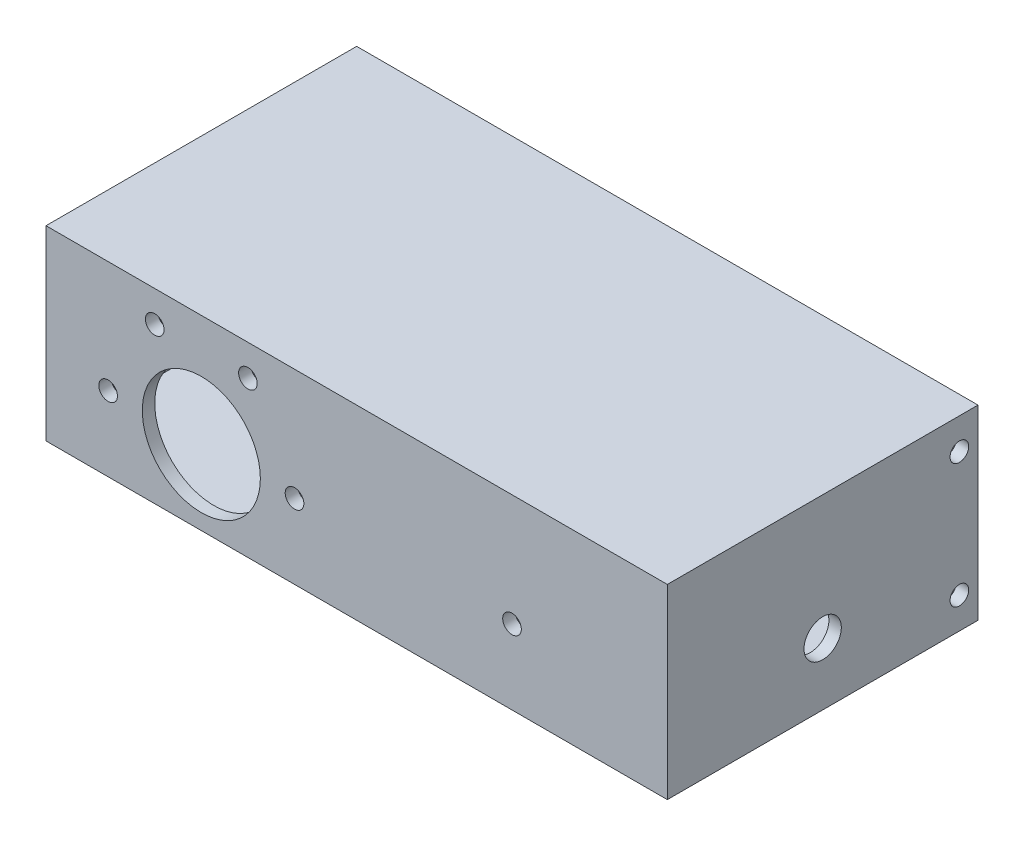
SolidWorks part; units mm, degrees
ref_plane "Front Plane" through (0, 0, 0) normal (0, 0, 1) x (1, 0, 0)
ref_plane "Top Plane" through (0, 0, 0) normal (0, 1, 0) x (1, 0, 0)
ref_plane "Right Plane" through (0, 0, 0) normal (1, 0, 0) x (0, 0, -1)
sketch "Sketch1" plane through (0, 0, 0) normal (0, 0, 1) x (1, 0, 0)
  line L0 (-40, -3) -> (-10, -3) construction
  line L1 (-50, -15) -> (50, -15)
  line L2 (-50, -15) -> (-50, 15)
  line L3 (-50, 15) -> (50, 15)
  line L4 (50, -15) -> (50, 15)
  line L5 (-50, -15) -> (50, 15) construction
  line L6 (-50, 15) -> (50, -15) construction
  circle A0 centre (-25, -3) radius 9.5
  arc A1 (-40, -3) -> (-10, -3) centre (-25, -3) cw construction
  circle A2 centre (-40, -3) radius 1.5
  circle A3 centre (-32.5, 9.9904) radius 1.5
  circle A4 centre (-17.5, 9.9904) radius 1.5
  circle A5 centre (-10, -3) radius 1.5
  circle A6 centre (25, -3) radius 1.5
  point P0 (0, 0)
  dimension "D1" = 19
  dimension "D7" = 3
  dimension "D12" = 3
  dimension "D2" = 100
  dimension "D3" = 30
  dimension "D4" = 12
  dimension "D5" = 25
  dimension "D6" = 30
  dimension "D9" = 12.9904
  dimension "D10" = 7.5
  dimension "D11" = 12.9904
  dimension "D13" = 12
  dimension "D14" = 25
  dimension "D8" = 4
extrude "Boss-Extrude1" add sketch "Sketch1" along normal blind 2
sketch "Sketch2" plane through (0, 0, 2) normal (0, 0, 1) x (1, 0, 0)
  line L0 (-48, 0) -> (-33, 0) construction
  line L1 (-37.5559, 12) -> (-20.1698, 12) construction
  line L2 (-20.1698, 12) -> (-12.0117, 12) construction
  line L3 (-12.6804, 0) -> (-5.2802, 0) construction
  line L4 (-50, -15) -> (50, -15) construction
  line L5 (-50, 15) -> (-50, -15) construction
  line L6 (25, 0) -> (40, 0)
  line L7 (40, 0) -> (15, 0) construction
  line L8 (50, -15) -> (50, 15) construction
  line L10 (50, 15) -> (-50, 15) construction
  line L11 (-48, -13) -> (48, -13)
  line L12 (-48, -13) -> (-48, 13)
  line L13 (-48, 13) -> (48, 13)
  line L14 (48, -13) -> (48, 13)
  line L15 (-48, -13) -> (48, 13) construction
  line L16 (-48, 13) -> (48, -13) construction
  line L18 (-50, -15) -> (50, -15)
  line L19 (-50, -15) -> (-50, 15)
  line L20 (-50, 15) -> (50, 15)
  line L21 (50, -15) -> (50, 15)
  line L22 (-50, -15) -> (50, 15) construction
  line L23 (-50, 15) -> (50, -15) construction
  text T0 "Disengaged" font "Century Gothic" height 1.5
  text T1 "        1" font "Century Gothic" height 1.5
  text T2 "   2" font "Century Gothic" height 1.5
  text T3 "    3" font "Century Gothic" height 1.5
  text T4 "Dead Mans Switch          " font "Century Gothic" height 1.5
  line M7 (50, -15) -> (50, 15)
  line M8 (50, 15) -> (-50, 15)
  line M9 (-50, 15) -> (-50, -15)
  line M10 (-50, -15) -> (50, -15)
  dimension "D1" = 15
  dimension "D2" = 27
  dimension "D3" = 2
  dimension "D4" = 12.4441
  dimension "D5" = 29.8302
  dimension "D6" = 37.3196
  dimension "D7" = 15
  dimension "D8" = 25
  dimension "D9" = 15
  dimension "D10" = 35
  dimension "D11" = 2
  dimension "D12" = 2
  dimension "D13" = 2
  dimension "D14" = 2
extrude "Boss-Extrude3" add sketch "Sketch2" against normal blind 50 contours L14 L11 L12 L13 M10 M7 M8 M9
sketch "Sketch3" plane through (0, 0, -48) normal (0, 0, -1) x (-1, 0, 0)
  line L1 (-50, -15) -> (50, -15)
  line L2 (-50, -15) -> (-50, 15)
  line L3 (-50, 15) -> (50, 15)
  line L4 (50, -15) -> (50, 15)
  line L5 (-50, -15) -> (50, 15) construction
  line L6 (-50, 15) -> (50, -15) construction
  point P0 (0, 0)
sketch "Sketch4" plane through (-50, 0, 0) normal (-1, 0, 0) x (0, 0, 1)
  line L0 (2, -15) -> (-48, -15) construction
  line L1 (-48, 15) -> (-48, -15) construction
  circle A0 centre (-38, 3) radius 5
  dimension "D1" = 10
  dimension "D2" = 18
  dimension "D3" = 10
extrude "Cut-Extrude1" cut sketch "Sketch4" against normal up to next
sketch "Sketch5" plane through (-50, 0, 0) normal (-1, 0, 0) x (0, 0, 1)
  line L0 (-48, -15) -> (-48, 15) construction
  line L1 (-48, 13) -> (-42, 13)
  line L2 (-48, 13) -> (-48, 7)
  line L3 (-48, 7) -> (-42, 7)
  line L4 (-42, 13) -> (-42, 7)
  line L5 (-45, 7) -> (-45, 13) construction
  line L6 (-48, 10) -> (-42, 10) construction
  line L7 (-48, 15) -> (-48, -15) construction
  line L8 (-48, -7) -> (-42, -7)
  line L9 (-48, -7) -> (-48, -13)
  line L10 (-48, -13) -> (-42, -13)
  line L11 (-42, -7) -> (-42, -13)
  line L12 (-45, -13) -> (-45, -7) construction
  line L13 (-48, -10) -> (-42, -10) construction
  line L14 (2, -15) -> (-48, -15) construction
  line L15 (2, 15) -> (-48, 15) construction
  circle A0 centre (-45, 10) radius 1.5
  circle A1 centre (-45, -10) radius 1.5
  point P96 (-45, 10)
  point P127 (-45, -10)
  dimension "D7" = 3
  dimension "D8" = 3
  dimension "D1" = 6
  dimension "D2" = 6
  dimension "D3" = 6
  dimension "D4" = 6
  dimension "D5" = 2
  dimension "D6" = 2
extrude "Cut-Extrude2" cut sketch "Sketch5" against normal through all contours A0 | A1
sketch "Sketch6" plane through (-50, 0, 0) normal (-1, 0, 0) x (0, 0, 1)
  line L0 (2, -15) -> (-48, -15) construction
  line L1 (2, 15) -> (2, -15) construction
  circle A0 centre (-23, -5) radius 3
  point P2 (0, 0)
  dimension "D1" = 6
  dimension "D2" = 10
  dimension "D3" = 25
extrude "Cut-Extrude3" cut sketch "Sketch6" against normal through all
